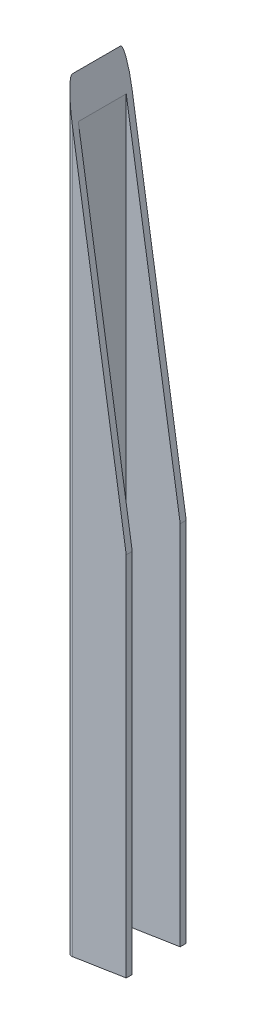
SolidWorks part; units mm, degrees
ref_plane "Спереди" through (0, 0, 0) normal (0, 0, 1) x (1, 0, 0)
ref_plane "Сверху" through (0, 0, 0) normal (0, 1, 0) x (1, 0, 0)
ref_plane "Справа" through (0, 0, 0) normal (1, 0, 0) x (0, 0, -1)
sketch "Эскиз1" plane through (0, 0, 0) normal (0, 1, 0) x (1, 0, 0)
  line L1 (-37, 15) -> (37, 15)
  line L2 (-40, 12) -> (-40, -12)
  line L3 (-37, -15) -> (37, -15)
  line L4 (40, 12) -> (40, -12)
  line L5 (-40, 15) -> (40, -15) construction
  line L6 (-40, -15) -> (40, 15) construction
  arc A0 (-37, 15) -> (-40, 12) centre (-37, 12) ccw
  arc A1 (-40, -12) -> (-37, -15) centre (-37, -12) ccw
  arc A2 (37, -15) -> (40, -12) centre (37, -12) ccw
  arc A3 (37, 15) -> (40, 12) centre (37, 12) cw
  point P0 (0, 0)
  dimension "D1" = 3
extrude "Вытянуть-Тонкостенный1" add sketch "Эскиз1" along normal blind 380 thin
sketch "Эскиз2" plane through (0, 380, 0) normal (0, 1, 0) x (1, 0, 0)
  line L1 (-10, -21.9251) -> (41.1465, -21.9251)
  line L2 (-10, -21.9251) -> (-10, 20.9728)
  line L3 (-10, 20.9728) -> (41.1465, 20.9728)
  line L4 (41.1465, -21.9251) -> (41.1465, 20.9728)
extrude "Вырез-Вытянуть1" cut sketch "Эскиз2" against normal through all
sketch "Эскиз3" plane through (0, 0, 15) normal (0, 0, 1) x (1, 0, 0)
  line L0 (-40, 380) -> (-10, 188.0753)
  line L1 (-10, 0) -> (-10, 380) construction
  line L2 (-10, 188.0753) -> (-10, 4.6893)
  line L3 (-10, 4.6893) -> (-40, 0)
  line L4 (-40, 0) -> (-40, 380)
  line L5 (67.3818, 16.785) -> (-80.8186, -6.3804) construction
  line L6 (-10, 380) -> (-10, 0) construction
extrude "Вырез-Вытянуть2" cut sketch "Эскиз3" against normal through all flip side to cut
